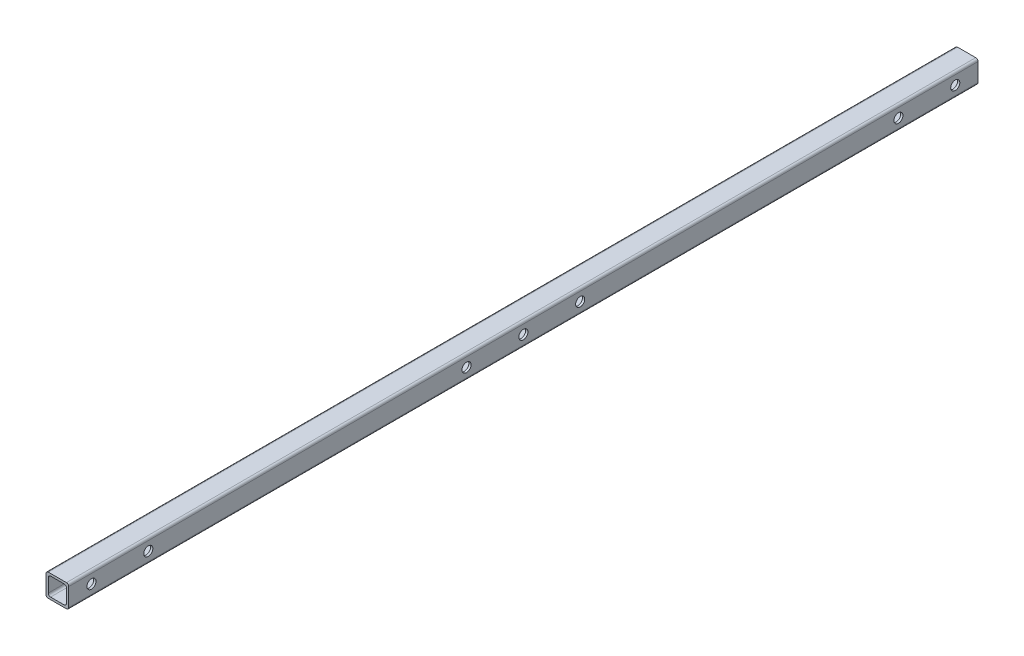
SolidWorks part; units mm, degrees
material "AISI 304"
ref_plane "Front Plane" through (0, 0, 0) normal (0, 0, 1) x (1, 0, 0)
ref_plane "Top Plane" through (0, 0, 0) normal (0, 1, 0) x (1, 0, 0)
ref_plane "Right Plane" through (0, 0, 0) normal (1, 0, 0) x (0, 0, -1)
sketch "Sketch1" plane through (0, 0, 0) normal (0, 0, 1) x (1, 0, 0)
  line L0 (1, 9) -> (9, 9)
  line L1 (0, 0) -> (10, 0)
  line L2 (0, 0) -> (0, 10)
  line L3 (0, 10) -> (10, 10)
  line L4 (10, 0) -> (10, 10)
  line L5 (9, 1) -> (9, 9)
  line L6 (1, 1) -> (9, 1)
  line L7 (1, 1) -> (1, 9)
  dimension "D1" = 10
  dimension "D2" = 1
extrude "Boss-Extrude1" add sketch "Sketch1" against normal blind 400
fillet "Fillet1" radius 1 8 edges at (0, 0, -200) (10, 0, -200) (0, 10, -200) (1, 9, -200) (9, 9, -200) (9, 1, -200) (1, 1, -200) (10, 10, -200)
sketch "Sketch2" plane through (10, 0, 0) normal (1, 0, 0) x (0, 0, -1)
  line L0 (0, 5) -> (400, 5) construction
  line L1 (0, 1) -> (0, 9) construction
  line L2 (400, 1) -> (400, 9) construction
  line L3 (200, 9) -> (200, 1) construction
  line L4 (400, 9) -> (0, 9) construction
  line L5 (0, 1) -> (400, 1) construction
  circle A0 centre (200, 5) radius 2
  circle A2 centre (225, 5) radius 2
  circle A3 centre (175, 5) radius 2
  circle A4 centre (10, 5) radius 2
  circle A5 centre (35, 5) radius 2
  circle A6 centre (390, 5) radius 2
  circle A7 centre (365, 5) radius 2
  dimension "D1" = 4
  dimension "D3" = 4
  dimension "D2" = 25
  dimension "D4" = 25
  dimension "D5" = 10
extrude "Cut-Extrude1" cut sketch "Sketch2" against normal blind 27
